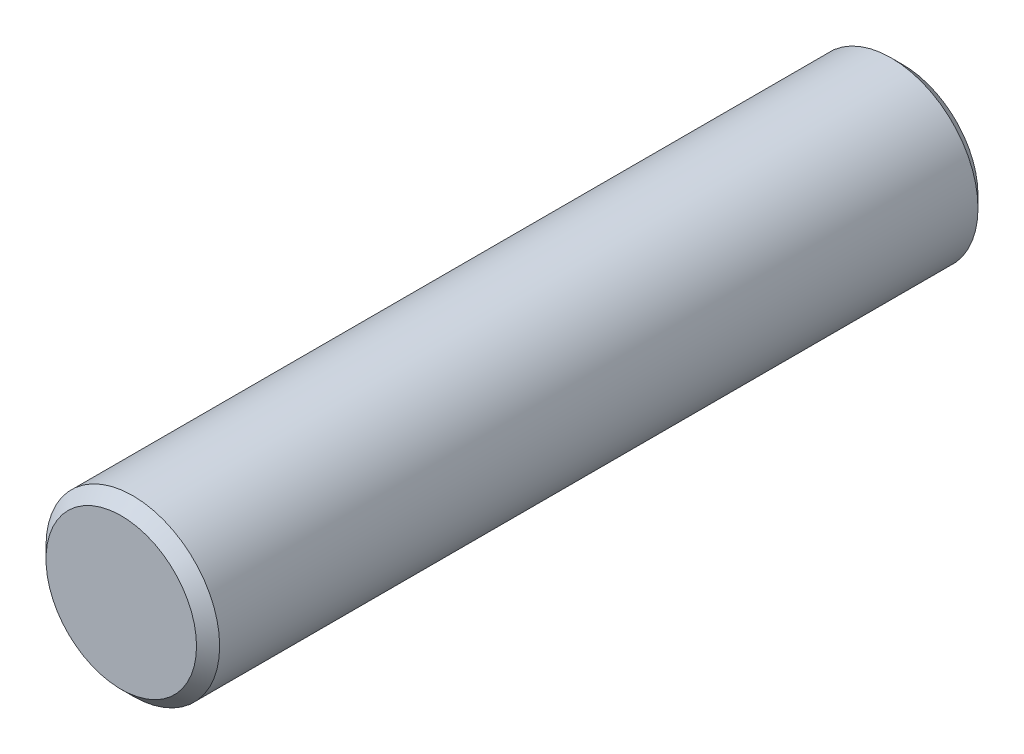
SolidWorks part; units mm, degrees
ref_plane "Front Plane" through (0, 0, 0) normal (0, 0, 1) x (1, 0, 0)
ref_plane "Top Plane" through (0, 0, 0) normal (0, 1, 0) x (1, 0, 0)
ref_plane "Right Plane" through (0, 0, 0) normal (1, 0, 0) x (0, 0, -1)
sketch "Sketch1" plane through (0, 0, 0) normal (0, 0, 1) x (1, 0, 0)
  circle A0 centre (0, 0) radius 1.5
  dimension "D1" = 3
extrude "Boss-Extrude1" add sketch "Sketch1" along normal blind 13.5
chamfer "Chamfer1" distance 0.2 angle 45 2 edges at (1.5, 0, 13.5) (1.5, 0, 0)
